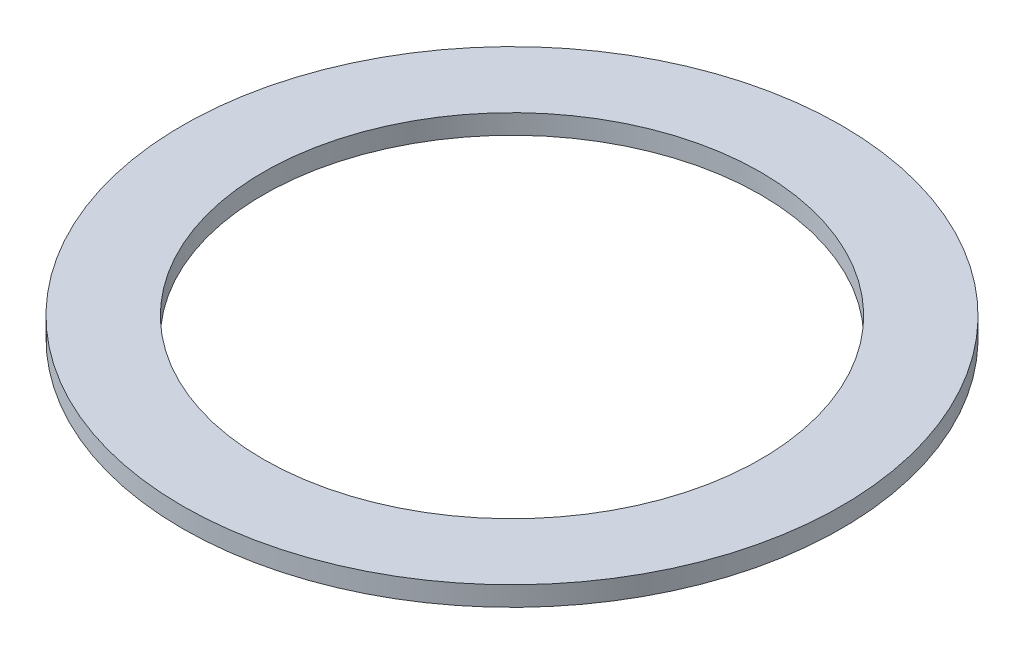
SolidWorks part; units mm, degrees
ref_plane "Front Plane" through (0, 0, 0) normal (0, 0, 1) x (1, 0, 0)
ref_plane "Top Plane" through (0, 0, 0) normal (0, 1, 0) x (1, 0, 0)
ref_plane "Right Plane" through (0, 0, 0) normal (1, 0, 0) x (0, 0, -1)
sketch "Sketch1" plane through (0, 0, 0) normal (0, 1, 0) x (1, 0, 0)
  circle A0 centre (0, 0) radius 84.15
  circle A1 centre (0, 0) radius 63.5
extrude "Carbon Felt Ring" add sketch "Sketch1" along normal blind 5
